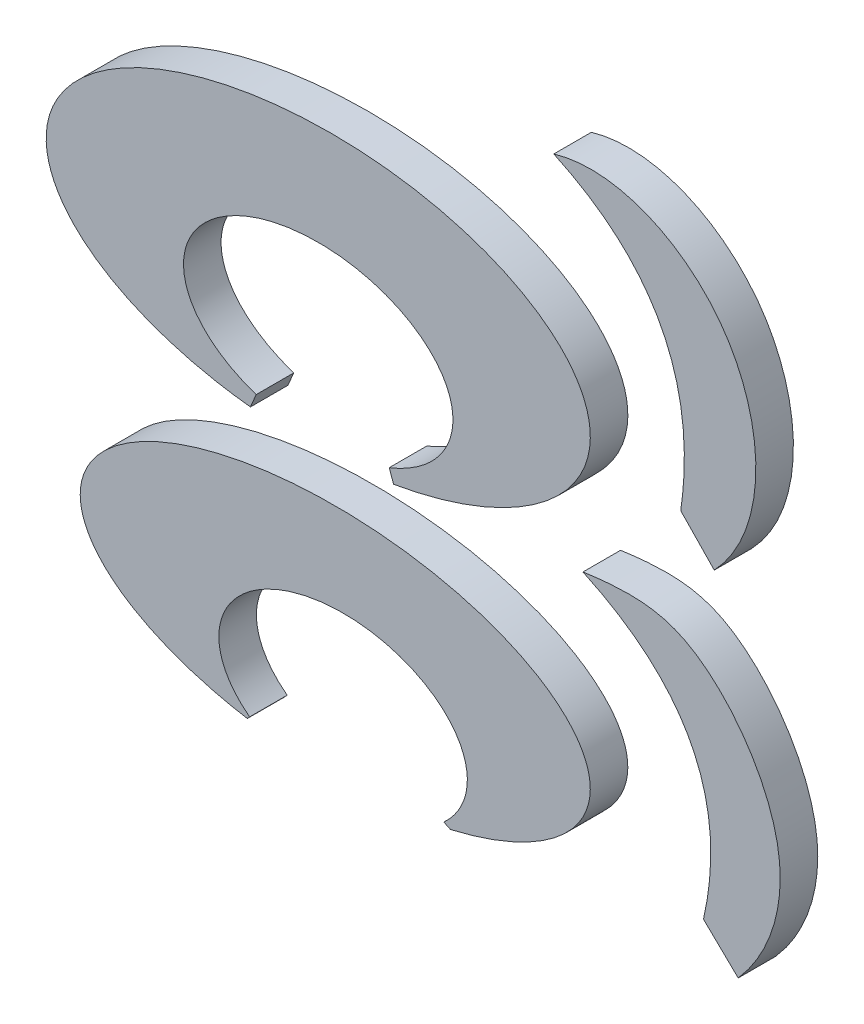
SolidWorks part; units mm, degrees
ref_plane "Front Plane" through (0, 0, 0) normal (0, 0, 1) x (1, 0, 0)
ref_plane "Top Plane" through (0, 0, 0) normal (0, 1, 0) x (1, 0, 0)
ref_plane "Right Plane" through (0, 0, 0) normal (1, 0, 0) x (0, 0, -1)
sketch "Sketch2" plane through (0, 0, 0) normal (0, 0, 1) x (1, 0, 0)
  line L0 (-8.3695, 3.4488) -> (-7.2355, 2.2743)
  line L1 (-7.6, -8.1339) -> (-6.4255, -9.2679)
  spline S0 degree 3 poles (-12.6624, 11.751) (-10.6129, 12.3585) (-5.5196, 10.1326) (-5.3339, 4.268) (-7.2355, 2.2743) knots 0 0 0 0 0.441262 1 1 1 1
  spline S1 degree 3 poles (-11.676, 0) (-9.837, 0.2641) (-7.4581, -0.0307) (-4.1962, -4.7475) (-5.3963, -8.1055) (-6.4255, -9.2679) knots 0 0 0 0 0.278031 0.664568 1 1 1 1
  spline S2 degree 3 poles (-17.1532, -1.3737) (-17.1948, -1.4568) (-17.0473, -1.5525) (-16.9562, -1.5707) (-16.2995, -1.702) (-15.6155, -1.7359) (-14.9861, -1.9647) (-14.3418, -2.199) (-13.6603, -2.3215) (-13.016, -2.5558) (-11.0765, -3.261) (-9.7451, -5.2332) (-10.2578, -7.284) (-10.5072, -8.2814) (-13.0318, -9.5779) (-13.804, -9.8452) (-17.9218, -11.2706) (-22.2354, -11.172) (-26.2157, -9.8452) (-29.1723, -8.8597) (-31.1635, -5.8313) (-28.1859, -3.5408) (-26.7311, -2.4218) (-25.2592, -2.373) (-23.6546, -1.5707) knots 9 9 9 9 10 10 10 11 11 11 12 12 12 13 13 13 14 14 14 15 15 15 16 16 16 17 17 17 17 construction
  spline S3 degree 3 poles (-23.6546, -1.5707) (-23.7203, -1.505) (-23.7635, -1.4031) (-23.8516, -1.3737) (-26.1044, -0.6228) (-30.7634, 0.3417) (-31.141, 3.5516) (-31.6075, 7.5163) (-25.4812, 9.6589) (-22.2755, 9.6589) (-20.3666, 9.6589) (-18.3732, 9.8686) (-16.5622, 9.2649) (-14.5852, 8.6059) (-12.4647, 8.2094) (-11.0459, 6.5068) (-10.6842, 6.0728) (-10.0961, 5.6915) (-10.0608, 5.1277) (-9.8973, 2.5108) (-11.1324, 0.8395) (-13.607, -0.1916) (-14.6232, -0.615) (-15.7149, -0.8286) (-16.7592, -1.1767) (-16.8985, -1.2231) (-17.0876, -1.2424) (-17.1532, -1.3737) knots 0 0 0 0 1 1 1 2 2 2 3 3 3 4 4 4 5 5 5 6 6 6 7 7 7 8 8 8 9 9 9 9 construction
  spline S4 degree 2 poles (-12.6624, 11.751) (-7.5124, 9.3555) (-8.3695, 3.4488) knots 0 0 0 1 1 1
  spline S5 degree 2 poles (-11.676, 0) (-6.32, -2.4853) (-7.6, -8.1339) knots 0 0 0 1 1 1
sketch "Sketch3" plane through (0, 0, 0) normal (0, 0, 1) x (1, 0, 0)
  line L0 (-22.7295, -0.331) -> (-22.9231, -0.7903)
  line L1 (-18.2278, -0.2209) -> (-18.0824, -0.6349)
  line L2 (-22.9505, -9.8828) -> (-23.0297, -9.9698)
  line L3 (-16.3811, -9.6768) -> (-16.1595, -9.7851)
  line L4 (-8.3695, 3.4488) -> (-7.2355, 2.2743)
  line L5 (-7.6, -8.1339) -> (-6.4255, -9.2679)
  ellipse E0 centre (-20.6298, 2.2599) end of major axis (-16.0737, 2.2599) minor radius 2.9195 (-18.2278, -0.2209) -> (-22.7295, -0.331) ccw
  ellipse E1 centre (-19.7894, -8.0466) end of major axis (-15.5871, -8.0466) minor radius 2.7868 (-16.3811, -9.6768) -> (-22.9505, -9.8828) ccw
  ellipse E2 centre (-20.6298, 3.8523) end of major axis (-11.4291, 4.162) minor radius 4.7334 (-18.0824, -0.6349) -> (-22.9231, -0.7903) ccw
  ellipse E3 centre (-20.0548, -6.233) end of major axis (-11.4291, -6.233) minor radius 3.9811 (-16.1595, -9.7851) -> (-23.0297, -9.9698) ccw
  ellipse E4 centre (-20.6298, 3.8523) end of major axis (-10.0475, 4.56) minor radius 5.8389 (-16.9601, -1.4624) -> (-24.1779, -1.8227) ccw construction
  ellipse E5 centre (-20.0548, -6.233) end of major axis (-29.9343, -6.5212) minor radius 4.9506 (-24.1779, -1.8227) -> (-16.9601, -1.4624) ccw construction
  spline S0 degree 3 poles (-23.6546, -1.5707) (-23.7203, -1.505) (-23.7635, -1.4031) (-23.8516, -1.3737) (-26.1044, -0.6228) (-30.7634, 0.3417) (-31.141, 3.5516) (-31.6075, 7.5163) (-25.4812, 9.6589) (-22.2755, 9.6589) (-20.3666, 9.6589) (-18.3732, 9.8686) (-16.5622, 9.2649) (-14.5852, 8.6059) (-12.4647, 8.2094) (-11.0459, 6.5068) (-10.6842, 6.0728) (-10.0961, 5.6915) (-10.0608, 5.1277) (-9.8973, 2.5108) (-11.1324, 0.8395) (-13.607, -0.1916) (-14.6232, -0.615) (-15.7149, -0.8286) (-16.7592, -1.1767) (-16.8985, -1.2231) (-17.0876, -1.2424) (-17.1532, -1.3737) knots 0 0 0 0 1 1 1 2 2 2 3 3 3 4 4 4 5 5 5 6 6 6 7 7 7 8 8 8 9 9 9 9 construction
  spline S1 degree 3 poles (-17.1532, -1.3737) (-17.1948, -1.4568) (-17.0473, -1.5525) (-16.9562, -1.5707) (-16.2995, -1.702) (-15.6155, -1.7359) (-14.9861, -1.9647) (-14.3418, -2.199) (-13.6603, -2.3215) (-13.016, -2.5558) (-11.0765, -3.261) (-9.7451, -5.2332) (-10.2578, -7.284) (-10.5072, -8.2814) (-13.0318, -9.5779) (-13.804, -9.8452) (-17.9218, -11.2706) (-22.2354, -11.172) (-26.2157, -9.8452) (-29.1723, -8.8597) (-31.1635, -5.8313) (-28.1859, -3.5408) (-26.7311, -2.4218) (-25.2592, -2.373) (-23.6546, -1.5707) knots 9 9 9 9 10 10 10 11 11 11 12 12 12 13 13 13 14 14 14 15 15 15 16 16 16 17 17 17 17 construction
  spline S2 degree 3 poles (-12.6624, 11.751) (-10.6129, 12.3585) (-5.5196, 10.1326) (-5.3339, 4.268) (-7.2355, 2.2743) knots 0 0 0 0 0.441262 1 1 1 1
  spline S3 degree 3 poles (-11.676, 0) (-9.837, 0.2641) (-7.4581, -0.0307) (-4.1962, -4.7475) (-5.3963, -8.1055) (-6.4255, -9.2679) knots 0 0 0 0 0.278031 0.664568 1 1 1 1
  spline S4 degree 2 poles (-12.6624, 11.751) (-7.5124, 9.3555) (-8.3695, 3.4488) knots 0 0 0 1 1 1
  spline S5 degree 2 poles (-11.676, 0) (-6.32, -2.4853) (-7.6, -8.1339) knots 0 0 0 1 1 1
sketch "Sketch4" plane through (0, 0, 0) normal (0, 0, 1) x (1, 0, 0)
  line L0 (-2.2589, 0.5473) -> (-2.4525, 0.088)
  line L1 (2.2428, 0.6575) -> (2.3882, 0.2435)
  line L2 (-2.4799, -9.0045) -> (-2.5591, -9.0915)
  line L3 (4.0896, -8.7984) -> (4.3111, -8.9067)
  ellipse E0 centre (-0.1592, 3.1382) end of major axis (4.3969, 3.1382) minor radius 2.9195 (2.2428, 0.6575) -> (-2.2589, 0.5473) ccw
  ellipse E1 centre (0.6812, -7.1683) end of major axis (-3.521, -7.1683) minor radius 2.7868 (4.0896, -8.7984) -> (-2.4799, -9.0045) ccw
  ellipse E2 centre (-0.1592, 4.7307) end of major axis (9.0415, 5.0403) minor radius 4.7334 (2.3882, 0.2435) -> (-2.4525, 0.088) ccw
  ellipse E3 centre (0.4158, -5.3547) end of major axis (9.0415, -5.3547) minor radius 3.9811 (4.3111, -8.9067) -> (-2.5591, -9.0915) ccw
  ellipse E4 centre (-0.1592, 4.7307) end of major axis (10.4231, 5.4383) minor radius 5.8389 (3.5105, -0.5841) -> (-3.7073, -0.9444) ccw
  ellipse E5 centre (0.4158, -5.3547) end of major axis (-9.4637, -5.6428) minor radius 4.9506 (-3.7073, -0.9444) -> (3.5105, -0.5841) ccw
extrude "Boss-Extrude1" [suppressed] add sketch "Sketch2" along normal blind 1.27
extrude "Boss-Extrude2" add sketch "Sketch3" along normal blind 1.27 separate body
sketch "Sketch5" plane through (0, 0, 1.27) normal (0, 0, 1) x (1, 0, 0)
  line L0 (-8.3695, 3.4488) -> (-7.2355, 2.2743) construction
  line L1 (-22.9231, -0.7903) -> (-22.7295, -0.331) construction
  line L2 (-18.2278, -0.2209) -> (-18.0824, -0.6349) construction
  line L3 (-16.3811, -9.6768) -> (-16.1595, -9.7851) construction
  line L4 (-23.0297, -9.9698) -> (-22.9505, -9.8828) construction
  line L5 (-7.6, -8.1339) -> (-6.4255, -9.2679) construction
  line L6 (-8.3695, 3.4488) -> (-7.2355, 2.2743)
  line L7 (-22.9231, -0.7903) -> (-22.7295, -0.331)
  line L8 (-18.2278, -0.2209) -> (-18.0824, -0.6349)
  line L9 (-16.3811, -9.6768) -> (-16.1595, -9.7851)
  line L10 (-23.0297, -9.9698) -> (-22.9505, -9.8828)
  line L11 (-7.6, -8.1339) -> (-6.4255, -9.2679)
  ellipse E0 centre (-20.6298, 3.8523) end of major axis (-11.4291, 4.162) minor radius 4.7334 (-18.0824, -0.6349) -> (-22.9231, -0.7903) ccw construction
  ellipse E1 centre (-20.6298, 2.2599) end of major axis (-16.0737, 2.2599) minor radius 2.9195 (-18.2278, -0.2209) -> (-22.7295, -0.331) ccw construction
  ellipse E2 centre (-19.7894, -8.0466) end of major axis (-15.5871, -8.0466) minor radius 2.7868 (-16.3811, -9.6768) -> (-22.9505, -9.8828) ccw construction
  ellipse E3 centre (-20.0548, -6.233) end of major axis (-11.4291, -6.233) minor radius 3.9811 (-16.1595, -9.7851) -> (-23.0297, -9.9698) ccw construction
  ellipse E4 centre (-20.6298, 3.8523) end of major axis (-11.4291, 4.162) minor radius 4.7334 (-18.0824, -0.6349) -> (-22.9231, -0.7903) ccw
  ellipse E5 centre (-20.6298, 2.2599) end of major axis (-16.0737, 2.2599) minor radius 2.9195 (-18.2278, -0.2209) -> (-22.7295, -0.331) ccw
  ellipse E6 centre (-19.7894, -8.0466) end of major axis (-15.5871, -8.0466) minor radius 2.7868 (-16.3811, -9.6768) -> (-22.9505, -9.8828) ccw
  ellipse E7 centre (-20.0548, -6.233) end of major axis (-11.4291, -6.233) minor radius 3.9811 (-16.1595, -9.7851) -> (-23.0297, -9.9698) ccw
  parabola Q0 (-12.6624, 11.751) -> (-8.3695, 3.4488) focus (-11.8731, 7.1822) apex (-9.1706, 8.7619) construction
  parabola Q1 (-11.676, 0) -> (-7.6, -8.1339) focus (-10.4703, -4.5866) apex (-7.9303, -3.3759) construction
  parabola Q2 (-12.6624, 11.751) -> (-8.3695, 3.4488) focus (-11.8731, 7.1822) apex (-9.1706, 8.7619)
  parabola Q3 (-11.676, 0) -> (-7.6, -8.1339) focus (-10.4703, -4.5866) apex (-7.9303, -3.3759)
  spline S0 degree 3 poles (-820.591, 1825.4636) (-119.1039, -138.3377) (127.5104, 107.1488) (-160.4176, -43.685) (1280.6645, -1509.5123) knots -4.852758 -4.852758 -4.852758 -4.852758 0.558738 5.583715 5.583715 5.583715 5.583715 only from (-7.2355, 2.2743) to (-12.6624, 11.751) construction
  spline S1 degree 3 poles (789.4377, 1820.8687) (-219.1702, -55.349) (13.2878, -30.0305) (-18.7104, 16.2407) (-40.2243, -73.1936) (-2010.7372, 20.584) knots -5.360141 -5.360141 -5.360141 -5.360141 0.335432 0.721969 4.44964 4.44964 4.44964 4.44964 only from (-6.4255, -9.2679) to (-11.676, 0) construction
  spline S2 degree 3 poles (-7.2355, 2.2743) (-5.3339, 4.268) (-5.5196, 10.1326) (-10.6129, 12.3585) (-12.6624, 11.751) knots 0 0 0 0 0.558738 1 1 1 1
  spline S3 degree 3 poles (-6.4255, -9.2679) (-5.3963, -8.1055) (-4.1962, -4.7475) (-7.4581, -0.0307) (-9.837, 0.2641) (-11.676, 0) knots 0 0 0 0 0.335432 0.721969 1 1 1 1
